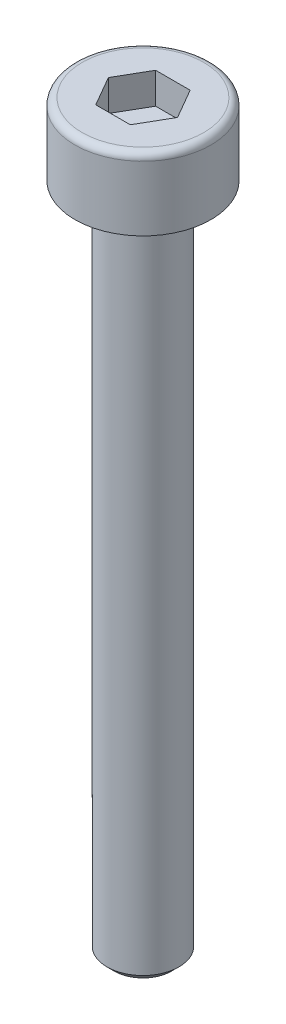
SolidWorks part; units mm, degrees
material "普通碳钢"
ref_plane "前视基准面" through (0, 0, 0) normal (0, 0, 1) x (1, 0, 0)
ref_plane "上视基准面" through (0, 0, 0) normal (0, 1, 0) x (1, 0, 0)
ref_plane "右视基准面" through (0, 0, 0) normal (1, 0, 0) x (0, 0, -1)
sketch "草图1" plane through (0, 0, 0) normal (0, 1, 0) x (1, 0, 0)
  circle A0 centre (0, 0) radius 2.84
extrude "凸台-拉伸1" add sketch "草图1" along normal blind 3
sketch "草图2" plane through (0, 3, 0) normal (0, 1, 0) x (1, 0, 0)
  line L1 (1.4434, 0) -> (0.7217, 1.25)
  line L2 (0.7217, 1.25) -> (-0.7217, 1.25)
  line L3 (-0.7217, 1.25) -> (-1.4434, 0)
  line L4 (-1.4434, 0) -> (-0.7217, -1.25)
  line L5 (-0.7217, -1.25) -> (0.7217, -1.25)
  line L6 (0.7217, -1.25) -> (1.4434, 0)
  circle A0 centre (0, 0) radius 1.25 construction
  dimension "D1" = 3
extrude "切除-拉伸1" cut sketch "草图2" against normal blind 1.3
sketch "草图3" plane through (0, 0, 0) normal (0, -1, 0) x (1, 0, 0)
  circle A0 centre (0, 0) radius 1.5
extrude "凸台-拉伸2" add sketch "草图3" along normal blind 28
cosmetic thread "装饰螺纹线1" parameters "D2"=1.567
chamfer "倒角1" distance 0.3 angle 45 1 edges at (0, -28, -1.5)
fillet "圆角1" radius 0.3 1 edges at (0, 3, 2.84)
chamfer "倒角2" distance 0.1 angle 45 1 edges at (0, 0, 1.5)
move or copy body "实体-移动/复制2" [suppressed] bodies to move or copy 108
move or copy body "实体-移动/复制3" [suppressed] bodies to move or copy 108
move or copy body "实体-移动/复制1" [suppressed] bodies to move or copy 108
equation "\"规格\"= 2"
equation "\"头部直径\"= 3.98"
equation "\"头部厚度\"= 2"
equation "\"内六角对边\"= 1.5"
equation "\"内六角深度\"= 1"
equation "\"螺纹长度\"= 4"
equation "\"D1@草图3\"=\"规格\""
equation "\"D1@草图1\"=\"头部直径\""
equation "\"D1@凸台-拉伸1\"=\"头部厚度\""
equation "\"D1@草图2\"=\"内六角对边\""
equation "\"D1@切除-拉伸1\"=\"内六角深度\""
equation "\"D1@凸台-拉伸2\"=\"螺纹长度\""
